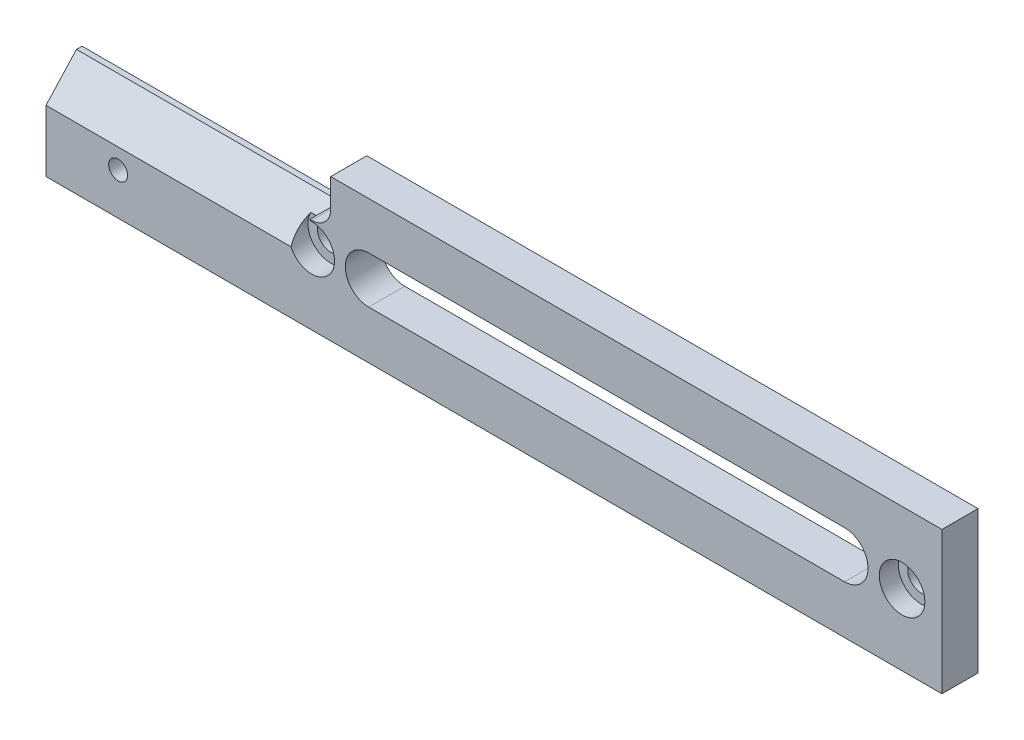
SolidWorks part; units mm, degrees
ref_plane "Front Plane" through (0, 0, 0) normal (0, 0, 1) x (1, 0, 0)
ref_plane "Top Plane" through (0, 0, 0) normal (0, 1, 0) x (1, 0, 0)
ref_plane "Right Plane" through (0, 0, 0) normal (1, 0, 0) x (0, 0, -1)
sketch "Sketch1" plane through (0, 0, 0) normal (0, 0, 1) x (1, 0, 0)
  line L0 (0, 0) -> (-119.888, 0)
  line L1 (-119.888, 0) -> (-119.888, 12.7)
  line L2 (-119.888, 12.7) -> (-84.328, 12.7)
  line L3 (-81.788, 15.24) -> (-81.788, 19.05)
  line L4 (-81.788, 19.05) -> (0, 19.05)
  line L5 (0, 19.05) -> (0, 0)
  arc A0 (-84.328, 12.7) -> (-81.788, 15.24) centre (-84.328, 15.24) ccw
  dimension "D5" = 2.54
  dimension "D1" = 19.05
  dimension "D2" = 119.888
  dimension "D3" = 81.788
  dimension "D4" = 12.7
extrude "Boss-Extrude1" add sketch "Sketch1" along normal blind 4.826
sketch "Sketch2" plane through (-119.888, 0, 0) normal (-1, 0, 0) x (0, 0, 1)
  line L0 (0.7498, 12.7) -> (4.826, 8.2587)
  line L1 (4.826, 12.7) -> (0, 12.7) construction
  line L2 (4.826, 12.7) -> (4.826, 0) construction
  line L3 (4.826, 8.2587) -> (4.826, 12.7)
  line L4 (4.826, 12.7) -> (0.7498, 12.7)
extrude "Cut-Extrude1" cut sketch "Sketch2" against normal blind 35.306
sketch "Sketch3" plane through (0, 0, 4.826) normal (0, 0, 1) x (1, 0, 0)
  line L0 (0, 0) -> (0, 19.05) construction
  line L1 (-119.888, 12.7) -> (-119.888, 0) construction
  circle A0 centre (-5.334, 9.525) radius 3.048
  circle A1 centre (-84.328, 9.525) radius 3.048
  point P2 (0, 9.525)
  point P7 (0, 0)
  point P8 (-119.888, 6.35)
  dimension "D1" = 6.096
  dimension "D2" = 5.334
  dimension "D3" = 6.096
  dimension "D4" = 35.56
extrude "Cut-Extrude2" cut sketch "Sketch3" against normal blind 2.54
sketch "Sketch4" plane through (0, 0, 4.826) normal (0, 0, 1) x (1, 0, 0)
  line L0 (-119.888, 8.2587) -> (-119.888, 0) construction
  line L1 (-119.888, 0) -> (0, 0) construction
  circle A0 centre (-5.334, 9.525) radius 1.778
  circle A1 centre (-84.328, 9.525) radius 1.778
  circle A2 centre (-110.236, 5.588) radius 1.27
  point P8 (-119.888, 4.1293)
  dimension "D1" = 3.556
  dimension "D2" = 3.556
  dimension "D3" = 2.54
  dimension "D4" = 9.652
  dimension "D5" = 5.588
extrude "Cut-Extrude3" cut sketch "Sketch4" against normal through all
sketch "Sketch5" plane through (0, 0, 4.826) normal (0, 0, 1) x (1, 0, 0)
  line L0 (-76.708, 12.7419) -> (-13.0302, 12.7419)
  line L1 (-13.0302, 6.4681) -> (-76.708, 6.4681)
  arc A0 (-76.708, 12.7419) -> (-76.708, 6.4681) centre (-76.708, 9.605) ccw
  arc A1 (-13.0302, 6.4681) -> (-13.0302, 12.7419) centre (-13.0302, 9.605) ccw
  arc A2 (-87.1005, 8.2587) -> (-84.582, 12.5624) centre (-84.328, 9.525) ccw construction
  dimension "D1" = 6.2738
  dimension "D2" = 63.6778
  dimension "D3" = 7.62
extrude "Cut-Extrude4" cut sketch "Sketch5" against normal through all
